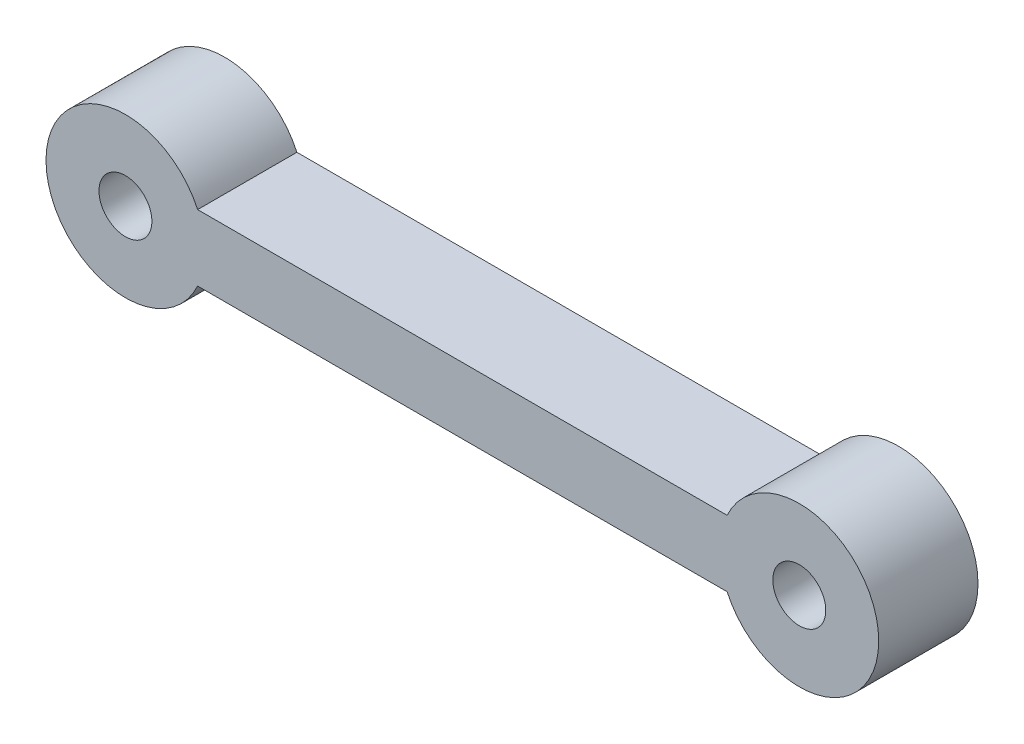
SolidWorks part; units mm, degrees
ref_plane "Front Plane" through (0, 0, 0) normal (0, 0, 1) x (1, 0, 0)
ref_plane "Top Plane" through (0, 0, 0) normal (0, 1, 0) x (1, 0, 0)
ref_plane "Right Plane" through (0, 0, 0) normal (1, 0, 0) x (0, 0, -1)
sketch "Sketch1" plane through (0, 0, 0) normal (0, 0, 1) x (1, 0, 0)
  line L0 (40, 0) -> (-40, 0)
  line L1 (-40, -10) -> (40, -10)
  line L2 (0, 10.1753) -> (0, -20.9744) construction
  arc A0 (-40, 0) -> (-40, -10) centre (-50.9087, -5) ccw
  circle A1 centre (-50.9087, -5) radius 4
  circle A2 centre (50.9087, -5) radius 4
  arc A3 (40, 0) -> (40, -10) centre (50.9087, -5) cw
  point P12 (0, -10)
  point P13 (0, 0)
  dimension "D1" = 12
  dimension "D2" = 8
  dimension "D3" = 5
  dimension "D4" = 10
  dimension "D5" = 40
extrude "Boss-Extrude1" add sketch "Sketch1" along normal blind 15
